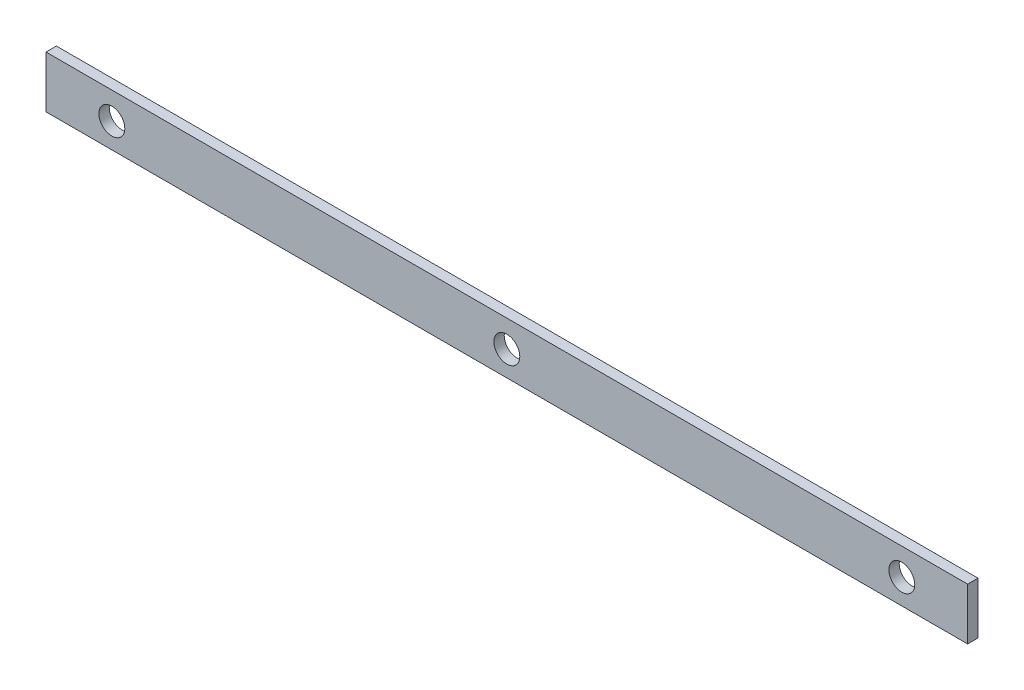
SolidWorks part; units mm, degrees
ref_plane "Front Plane" through (0, 0, 0) normal (0, 0, 1) x (1, 0, 0)
ref_plane "Top Plane" through (0, 0, 0) normal (0, 1, 0) x (1, 0, 0)
ref_plane "Right Plane" through (0, 0, 0) normal (1, 0, 0) x (0, 0, -1)
sketch "Sketch1" plane through (0, 0, 0) normal (0, 0, 1) x (1, 0, 0)
  line L1 (-45.4769, -4.8097) -> (132.3231, -4.8097)
  line L2 (-45.4769, -4.8097) -> (-45.4769, 5.1903)
  line L3 (-45.4769, 5.1903) -> (132.3231, 5.1903)
  line L4 (132.3231, -4.8097) -> (132.3231, 5.1903)
  dimension "D1" = 177.8
  dimension "D2" = 10
extrude "Boss-Extrude1" add sketch "Sketch1" along normal blind 2
hole_wizard "Ø5.0 (5) Diameter Hole1" positions "Sketch3" profile "Sketch2" hole size "Ø5.0" standard "ANSI Metric"
sketch "Sketch3" plane through (0, 0, 2) normal (0, 0, 1) x (1, 0, 0)
  line L0 (-45.4769, 5.1903) -> (-45.4769, -4.8097) construction
  point P0 (-32.7769, 0)
  point P2 (43.4231, 0)
  point P4 (119.6231, 0)
  dimension "D1" = 12.7
  dimension "D2" = 76.2
  dimension "D3" = 76.2
sketch "Sketch2" plane through (-32.7769, 0, 2) normal (1, 0, 0) x (0, -1, 0)
  line L0 (0, 0) -> (0, 6.5022)
  line L1 (0, 6.5022) -> (2.5, 5)
  line L2 (2.5, 5) -> (2.5, 0)
  line L5 (2.5, 0) -> (0, 0)
  line L10 (0, 6.5022) -> (-2.5, 5) construction
  line L11 (0, -6.35) -> (0, 107.95) construction
  dimension "Hole Dia." = 5
  dimension "Hole Depth" = 5
  dimension "Drill Angle" = 118
